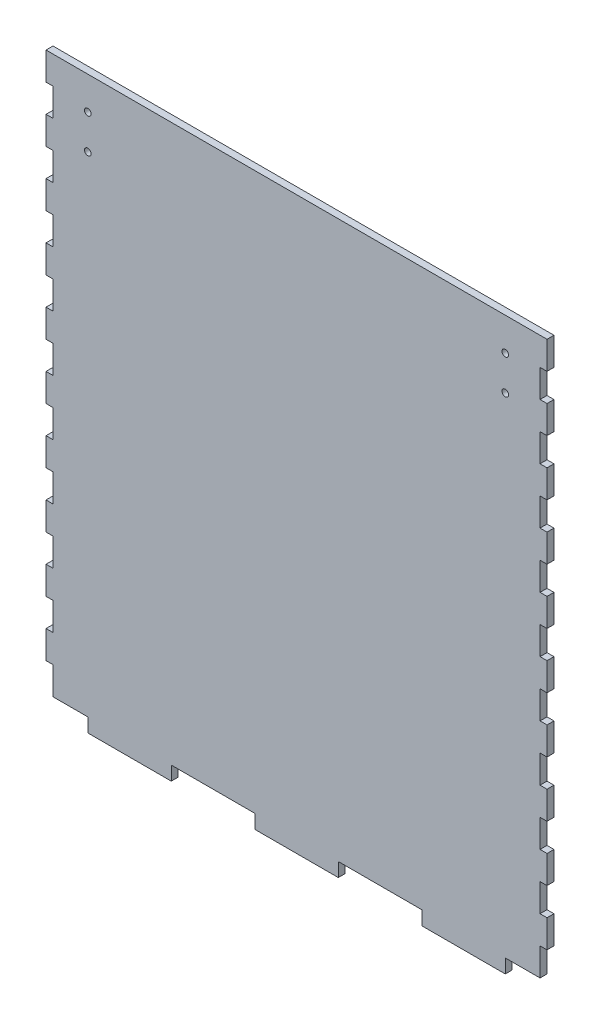
SolidWorks part; units mm, degrees
material "Acrylic (Medium-high impact)"
ref_plane "Front Plane" through (0, 0, 0) normal (0, 0, 1) x (1, 0, 0)
ref_plane "Top Plane" through (0, 0, 0) normal (0, 1, 0) x (1, 0, 0)
ref_plane "Right Plane" through (0, 0, 0) normal (1, 0, 0) x (0, 0, -1)
sketch "Sketch1" plane through (0, 0, 0) normal (0, 0, 1) x (1, 0, 0)
  line L0 (-114.3, 114.3) -> (-111.125, 114.3)
  line L1 (-114.3, 127) -> (114.3, 127)
  line L2 (-114.3, 127) -> (-114.3, -127)
  line L3 (-114.3, -127) -> (114.3, -127)
  line L4 (114.3, 127) -> (114.3, -127)
  line L5 (-114.3, 127) -> (-111.125, 127)
  line L6 (-114.3, 127) -> (-114.3, 114.3)
  line L7 (-114.3, 114.3) -> (-111.125, 114.3)
  line L8 (-111.125, 127) -> (-111.125, 114.3)
  line L9 (-114.3, 114.3) -> (-114.3, 101.6)
  line L10 (-114.3, 101.6) -> (-111.125, 101.6)
  line L11 (-111.125, 114.3) -> (-111.125, 101.6)
  line L12 (-114.3, 101.6) -> (-111.125, 101.6)
  line L13 (-114.3, 101.6) -> (-114.3, 88.9)
  line L14 (-114.3, 88.9) -> (-111.125, 88.9)
  line L15 (-111.125, 101.6) -> (-111.125, 88.9)
  line L16 (-114.3, 88.9) -> (-111.125, 88.9)
  line L17 (-114.3, 88.9) -> (-114.3, 76.2)
  line L18 (-114.3, 76.2) -> (-111.125, 76.2)
  line L19 (-111.125, 88.9) -> (-111.125, 76.2)
  line L20 (-114.3, 76.2) -> (-111.125, 76.2)
  line L21 (-114.3, 76.2) -> (-114.3, 63.5)
  line L22 (-114.3, 63.5) -> (-111.125, 63.5)
  line L23 (-111.125, 76.2) -> (-111.125, 63.5)
  line L24 (-114.3, 63.5) -> (-111.125, 63.5)
  line L25 (-114.3, 63.5) -> (-114.3, 50.8)
  line L26 (-114.3, 50.8) -> (-111.125, 50.8)
  line L27 (-111.125, 63.5) -> (-111.125, 50.8)
  line L28 (-114.3, 50.8) -> (-111.125, 50.8)
  line L29 (-114.3, 50.8) -> (-114.3, 38.1)
  line L30 (-114.3, 38.1) -> (-111.125, 38.1)
  line L31 (-111.125, 50.8) -> (-111.125, 38.1)
  line L32 (-114.3, 38.1) -> (-111.125, 38.1)
  line L33 (-114.3, 38.1) -> (-114.3, 25.4)
  line L34 (-114.3, 25.4) -> (-111.125, 25.4)
  line L35 (-111.125, 38.1) -> (-111.125, 25.4)
  line L36 (-114.3, 25.4) -> (-111.125, 25.4)
  line L37 (-114.3, 25.4) -> (-114.3, 12.7)
  line L38 (-114.3, 12.7) -> (-111.125, 12.7)
  line L39 (-111.125, 25.4) -> (-111.125, 12.7)
  line L40 (-114.3, 12.7) -> (-111.125, 12.7)
  line L41 (-114.3, 12.7) -> (-114.3, 0)
  line L42 (-114.3, 0) -> (-111.125, 0)
  line L43 (-111.125, 12.7) -> (-111.125, 0)
  line L44 (-114.3, 0) -> (-111.125, 0)
  line L45 (-114.3, 0) -> (-114.3, -12.7)
  line L46 (-114.3, -12.7) -> (-111.125, -12.7)
  line L47 (-111.125, 0) -> (-111.125, -12.7)
  line L48 (-114.3, -12.7) -> (-111.125, -12.7)
  line L49 (-114.3, -12.7) -> (-114.3, -25.4)
  line L50 (-114.3, -25.4) -> (-111.125, -25.4)
  line L51 (-111.125, -12.7) -> (-111.125, -25.4)
  line L52 (-114.3, -25.4) -> (-111.125, -25.4)
  line L53 (-114.3, -25.4) -> (-114.3, -38.1)
  line L54 (-114.3, -38.1) -> (-111.125, -38.1)
  line L55 (-111.125, -25.4) -> (-111.125, -38.1)
  line L56 (-114.3, -38.1) -> (-111.125, -38.1)
  line L57 (-114.3, -38.1) -> (-114.3, -50.8)
  line L58 (-114.3, -50.8) -> (-111.125, -50.8)
  line L59 (-111.125, -38.1) -> (-111.125, -50.8)
  line L60 (-114.3, -50.8) -> (-111.125, -50.8)
  line L61 (-114.3, -50.8) -> (-114.3, -63.5)
  line L62 (-114.3, -63.5) -> (-111.125, -63.5)
  line L63 (-111.125, -50.8) -> (-111.125, -63.5)
  line L64 (-114.3, -63.5) -> (-111.125, -63.5)
  line L65 (-114.3, -63.5) -> (-114.3, -76.2)
  line L66 (-114.3, -76.2) -> (-111.125, -76.2)
  line L67 (-111.125, -63.5) -> (-111.125, -76.2)
  line L68 (-114.3, -76.2) -> (-111.125, -76.2)
  line L69 (-114.3, -76.2) -> (-114.3, -88.9)
  line L70 (-114.3, -88.9) -> (-111.125, -88.9)
  line L71 (-111.125, -76.2) -> (-111.125, -88.9)
  line L72 (-114.3, -88.9) -> (-111.125, -88.9)
  line L73 (-114.3, -88.9) -> (-114.3, -101.6)
  line L74 (-114.3, -101.6) -> (-111.125, -101.6)
  line L75 (-111.125, -88.9) -> (-111.125, -101.6)
  line L76 (-114.3, -101.6) -> (-111.125, -101.6)
  line L77 (-114.3, -101.6) -> (-114.3, -114.3)
  line L78 (-114.3, -114.3) -> (-111.125, -114.3)
  line L79 (-111.125, -101.6) -> (-111.125, -114.3)
  line L80 (-114.3, -114.3) -> (-111.125, -114.3)
  line L81 (-114.3, -114.3) -> (-114.3, -127)
  line L82 (-114.3, -127) -> (-111.125, -127)
  line L83 (-111.125, -114.3) -> (-111.125, -127)
  line L100 (0, 127) -> (0, -127) construction
  line L101 (114.3, 114.3) -> (111.125, 114.3)
  line L102 (114.3, 127) -> (111.125, 127)
  line L103 (114.3, 127) -> (114.3, 114.3)
  line L104 (114.3, 114.3) -> (111.125, 114.3)
  line L105 (111.125, 127) -> (111.125, 114.3)
  line L106 (114.3, 114.3) -> (114.3, 101.6)
  line L107 (114.3, 101.6) -> (111.125, 101.6)
  line L108 (111.125, 114.3) -> (111.125, 101.6)
  line L109 (114.3, 101.6) -> (111.125, 101.6)
  line L110 (114.3, 101.6) -> (114.3, 88.9)
  line L111 (114.3, 88.9) -> (111.125, 88.9)
  line L112 (111.125, 101.6) -> (111.125, 88.9)
  line L113 (114.3, 88.9) -> (111.125, 88.9)
  line L114 (114.3, 88.9) -> (114.3, 76.2)
  line L115 (114.3, 76.2) -> (111.125, 76.2)
  line L116 (111.125, 88.9) -> (111.125, 76.2)
  line L117 (114.3, 76.2) -> (111.125, 76.2)
  line L118 (114.3, 76.2) -> (114.3, 63.5)
  line L119 (114.3, 63.5) -> (111.125, 63.5)
  line L120 (111.125, 76.2) -> (111.125, 63.5)
  line L121 (114.3, 63.5) -> (111.125, 63.5)
  line L122 (114.3, 63.5) -> (114.3, 50.8)
  line L123 (114.3, 50.8) -> (111.125, 50.8)
  line L124 (111.125, 63.5) -> (111.125, 50.8)
  line L125 (114.3, 50.8) -> (111.125, 50.8)
  line L126 (114.3, 50.8) -> (114.3, 38.1)
  line L127 (114.3, 38.1) -> (111.125, 38.1)
  line L128 (111.125, 50.8) -> (111.125, 38.1)
  line L129 (114.3, 38.1) -> (111.125, 38.1)
  line L130 (114.3, 38.1) -> (114.3, 25.4)
  line L131 (114.3, 25.4) -> (111.125, 25.4)
  line L132 (111.125, 38.1) -> (111.125, 25.4)
  line L133 (114.3, 25.4) -> (111.125, 25.4)
  line L134 (114.3, 25.4) -> (114.3, 12.7)
  line L135 (114.3, 12.7) -> (111.125, 12.7)
  line L136 (111.125, 25.4) -> (111.125, 12.7)
  line L137 (114.3, 12.7) -> (111.125, 12.7)
  line L138 (114.3, 12.7) -> (114.3, 0)
  line L139 (114.3, 0) -> (111.125, 0)
  line L140 (111.125, 12.7) -> (111.125, 0)
  line L141 (114.3, 0) -> (111.125, 0)
  line L142 (114.3, 0) -> (114.3, -12.7)
  line L143 (114.3, -12.7) -> (111.125, -12.7)
  line L144 (111.125, 0) -> (111.125, -12.7)
  line L145 (114.3, -12.7) -> (111.125, -12.7)
  line L146 (114.3, -12.7) -> (114.3, -25.4)
  line L147 (114.3, -25.4) -> (111.125, -25.4)
  line L148 (111.125, -12.7) -> (111.125, -25.4)
  line L149 (114.3, -25.4) -> (111.125, -25.4)
  line L150 (114.3, -25.4) -> (114.3, -38.1)
  line L151 (114.3, -38.1) -> (111.125, -38.1)
  line L152 (111.125, -25.4) -> (111.125, -38.1)
  line L153 (114.3, -38.1) -> (111.125, -38.1)
  line L154 (114.3, -38.1) -> (114.3, -50.8)
  line L155 (114.3, -50.8) -> (111.125, -50.8)
  line L156 (111.125, -38.1) -> (111.125, -50.8)
  line L157 (114.3, -50.8) -> (111.125, -50.8)
  line L158 (114.3, -50.8) -> (114.3, -63.5)
  line L159 (114.3, -63.5) -> (111.125, -63.5)
  line L160 (111.125, -50.8) -> (111.125, -63.5)
  line L161 (114.3, -63.5) -> (111.125, -63.5)
  line L162 (114.3, -63.5) -> (114.3, -76.2)
  line L163 (114.3, -76.2) -> (111.125, -76.2)
  line L164 (111.125, -63.5) -> (111.125, -76.2)
  line L165 (114.3, -76.2) -> (111.125, -76.2)
  line L166 (114.3, -76.2) -> (114.3, -88.9)
  line L167 (114.3, -88.9) -> (111.125, -88.9)
  line L168 (111.125, -76.2) -> (111.125, -88.9)
  line L169 (114.3, -88.9) -> (111.125, -88.9)
  line L170 (114.3, -88.9) -> (114.3, -101.6)
  line L171 (114.3, -101.6) -> (111.125, -101.6)
  line L172 (111.125, -88.9) -> (111.125, -101.6)
  line L173 (114.3, -101.6) -> (111.125, -101.6)
  line L174 (114.3, -101.6) -> (114.3, -114.3)
  line L175 (114.3, -114.3) -> (111.125, -114.3)
  line L176 (111.125, -101.6) -> (111.125, -114.3)
  line L177 (114.3, -114.3) -> (111.125, -114.3)
  line L178 (114.3, -114.3) -> (114.3, -127)
  line L179 (114.3, -127) -> (111.125, -127)
  line L180 (111.125, -114.3) -> (111.125, -127)
  line L183 (95.25, -127) -> (95.25, -133.35)
  line L184 (95.25, -133.35) -> (57.15, -133.35)
  line L185 (57.15, -133.35) -> (57.15, -127)
  line L186 (57.15, -127) -> (95.25, -127)
  line L188 (-19.05, -127) -> (19.05, -127)
  line L189 (19.05, -127) -> (19.05, -133.35)
  line L190 (19.05, -133.35) -> (-19.05, -133.35)
  line L191 (-19.05, -133.35) -> (-19.05, -127)
  line L192 (-95.25, -127) -> (-57.15, -127)
  line L193 (-57.15, -127) -> (-57.15, -133.35)
  line L194 (-57.15, -133.35) -> (-95.25, -133.35)
  line L195 (-95.25, -133.35) -> (-95.25, -127)
  point P4 (0, 127)
  point P6 (-114.3, 0)
  dimension "D1" = 254
  dimension "D2" = 228.6
  dimension "D3" = 12.7
  dimension "D4" = 3.175
  dimension "D7" = 6.35
  dimension "D8" = 38.1
  dimension "D9" = 19.05
  dimension "D11" = 19.05
  dimension "D5" = 20
  dimension "D6" = 20
  dimension "D10" = 3
extrude "Boss-Extrude1" add sketch "Sketch1" along normal blind 3.175 contours L100 L1 L8 L11 L15 L19 L23 L27 L31 L35 L39 L43 L47 L51 L55 L59 L63 L67 L71 L75 L79 L83 L3 | L1 L100 L3 L180 L176 L172 L168 L164 L160 L156 L152 L148 L144 L140 L136 L132 L128 L124 L120 L116 L112 L108 L105 | L1 L105 L101 L4 | L107 L112 L111 L4 | L115 L120 L119 L4 | L123 L128 L127 L4 | L131 L136 L135 L4 | L139 L144 L143 L4 | L147 L152 L151 L4 | L155 L160 L159 L4 | L163 L168 L167 L4 | L171 L176 L175 L4 | L8 L1 L2 L0 | L15 L10 L2 L14 | L23 L18 L2 L22 | L31 L26 L2 L30 | L63 L58 L2 L62 | L71 L66 L2 L70 | L79 L74 L2 L78 | L185 L184 L183 L3 | L191 L190 L189 L188 L3 | L195 L194 L193 L3
sketch "Sketch3" plane through (0, 0, 0) normal (0, 0, -1) x (-1, 0, 0)
  line L0 (0, 127) -> (0, -133.35) construction
  line L1 (114.3, 127) -> (-114.3, 127) construction
  line L2 (-19.05, -133.35) -> (19.05, -133.35) construction
  line L3 (-114.3, 127) -> (-114.3, 114.3) construction
  circle A0 centre (-95.25, 112) radius 1.5
  circle A1 centre (-95.25, 96.25) radius 1.5
  circle A2 centre (95.25, 96.25) radius 1.5
  circle A3 centre (95.25, 112) radius 1.5
  point P12 (0, 0)
  dimension "D1" = 3
  dimension "D2" = 3
  dimension "D3" = 15.75
  dimension "D4" = 15
  dimension "D5" = 19.05
extrude "Cut-Extrude1" cut sketch "Sketch3" against normal up to surface (3.175 mm away) up to face at (0, -16.9793, 3.175)
